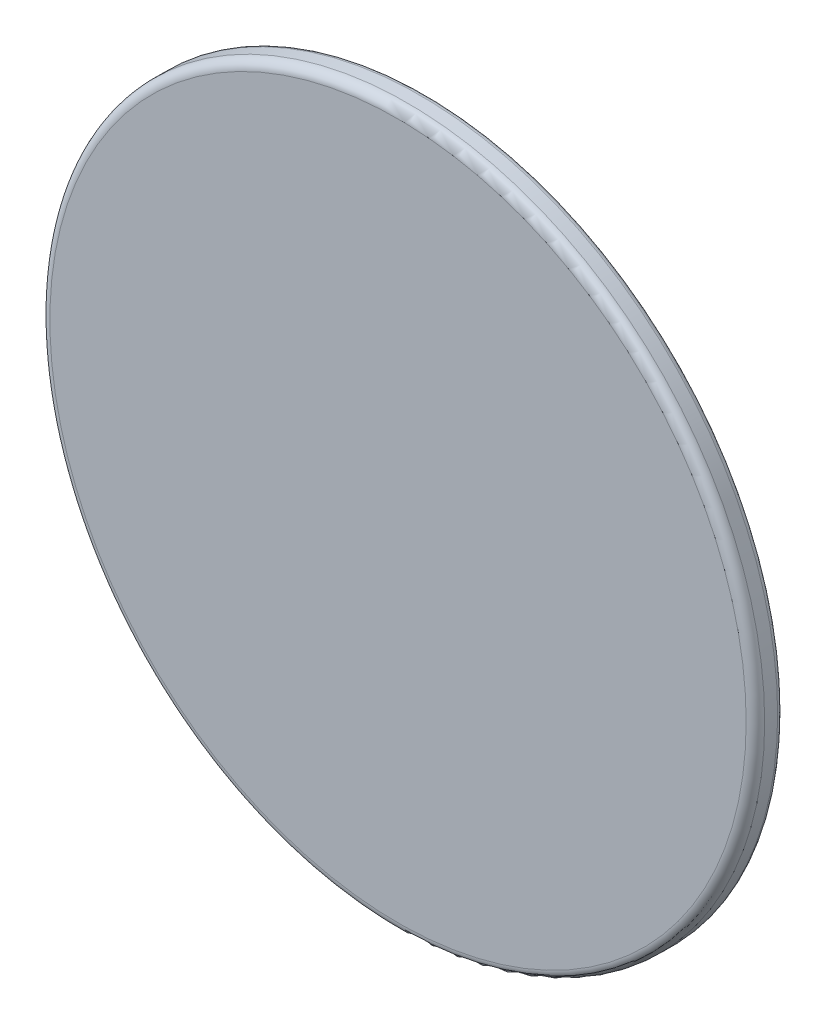
SolidWorks part; units mm, degrees
ref_plane "Face" through (0, 0, 0) normal (0, 0, 1) x (1, 0, 0)
ref_plane "Dessus" through (0, 0, 0) normal (0, 1, 0) x (1, 0, 0)
ref_plane "Droite" through (0, 0, 0) normal (1, 0, 0) x (0, 0, -1)
sketch "Esquisse1" plane through (0, 0, 0) normal (0, 0, 1) x (1, 0, 0)
  circle A0 centre (0, 0) radius 19.3
  dimension "D1" = 38.6
extrude "Boss.-Extru.1" add sketch "Esquisse1" along normal blind 1.5
sketch "Esquisse3" plane through (0, 0, 0) normal (0, 0, -1) x (-1, 0, 0)
  circle A0 centre (0, 0) radius 18
  dimension "D1" = 36
extrude "Enlèv. mat.-Extru.2" cut sketch "Esquisse3" against normal blind 1
fillet "Congé1" radius 0.5 1 edges at (19.3, 0, 1.5)
fillet "Congé2" radius 0.3 1 edges at (19.3, 0, 0)
